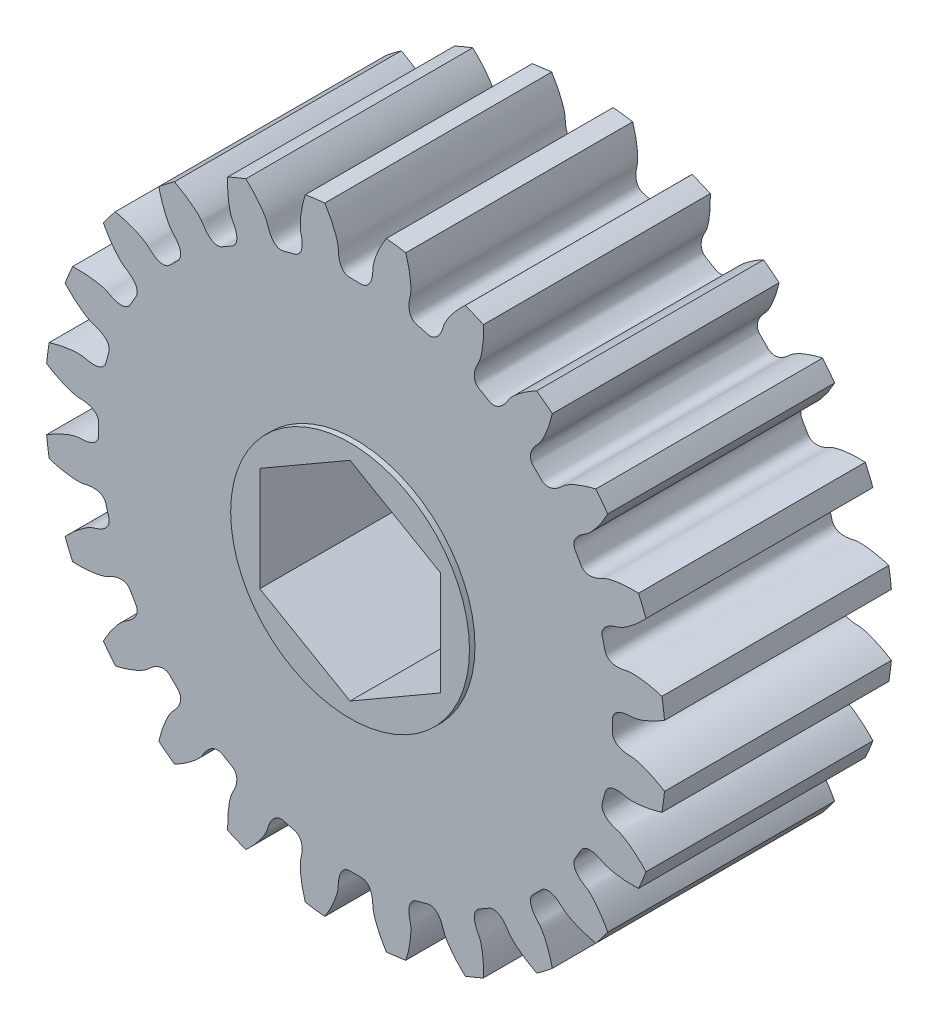
SolidWorks part; units mm, degrees
ref_plane "Front Plane" through (0, 0, 0) normal (0, 0, 1) x (1, 0, 0)
ref_plane "Top Plane" through (0, 0, 0) normal (0, 1, 0) x (1, 0, 0)
ref_plane "Right Plane" through (0, 0, 0) normal (1, 0, 0) x (0, 0, -1)
ref_plane "Plane1" through (0, 0, -6.0325) normal (0, 0, -1) x (-1, 0, 0)
sketch "Sketch1" plane through (0, 0, -6.0325) normal (0, 0, -1) x (-1, 0, 0)
  arc A0 (-12.7729, 10.461) -> (-13.4104, 9.6302) centre (0, 0) ccw
  arc A1 (-15.0452, 6.7987) -> (-15.446, 5.8312) centre (0, 0) ccw
  arc A2 (-16.2922, 2.673) -> (-16.4289, 1.6348) centre (0, 0) ccw
  arc A3 (-16.4289, -1.6348) -> (-16.2922, -2.673) centre (0, 0) ccw
  arc A4 (-15.446, -5.8312) -> (-15.0452, -6.7987) centre (0, 0) ccw
  arc A5 (-13.4104, -9.6302) -> (-12.7729, -10.461) centre (0, 0) ccw
  arc A6 (-10.461, -12.7729) -> (-9.6302, -13.4104) centre (0, 0) ccw
  arc A7 (-6.7987, -15.0452) -> (-5.8312, -15.446) centre (0, 0) ccw
  arc A8 (-2.673, -16.2922) -> (-1.6348, -16.4289) centre (0, 0) ccw
  arc A9 (1.6348, -16.4289) -> (2.673, -16.2922) centre (0, 0) ccw
  arc A10 (5.8312, -15.446) -> (6.7987, -15.0452) centre (0, 0) ccw
  arc A11 (9.6302, -13.4104) -> (10.461, -12.7729) centre (0, 0) ccw
  arc A12 (12.7729, -10.461) -> (13.4104, -9.6302) centre (0, 0) ccw
  arc A13 (15.0452, -6.7987) -> (15.446, -5.8312) centre (0, 0) ccw
  arc A14 (16.2922, -2.673) -> (16.4289, -1.6348) centre (0, 0) ccw
  arc A15 (16.4289, 1.6348) -> (16.2922, 2.673) centre (0, 0) ccw
  arc A16 (15.446, 5.8312) -> (15.0452, 6.7987) centre (0, 0) ccw
  arc A17 (13.4104, 9.6302) -> (12.7729, 10.461) centre (0, 0) ccw
  arc A18 (10.461, 12.7729) -> (9.6302, 13.4104) centre (0, 0) ccw
  arc A19 (6.7987, 15.0452) -> (5.8312, 15.446) centre (0, 0) ccw
  arc A20 (2.673, 16.2922) -> (1.6348, 16.4289) centre (0, 0) ccw
  arc A21 (-1.6348, 16.4289) -> (-2.673, 16.2922) centre (0, 0) ccw
  arc A22 (-5.8312, 15.446) -> (-6.7987, 15.0452) centre (0, 0) ccw
  arc A23 (-9.6302, 13.4104) -> (-10.461, 12.7729) centre (0, 0) ccw
  spline S0 degree 3 number of poles 101 (-15.0452, 6.7987) -> (-13.4104, 9.6302)
  spline S1 degree 3 number of poles 101 (-16.2922, 2.673) -> (-15.446, 5.8312)
  spline S2 degree 3 number of poles 101 (-16.4289, -1.6348) -> (-16.4289, 1.6348)
  spline S3 degree 3 number of poles 101 (-15.446, -5.8312) -> (-16.2922, -2.673)
  spline S4 degree 3 number of poles 101 (-13.4104, -9.6302) -> (-15.0452, -6.7987)
  spline S5 degree 3 number of poles 101 (-10.461, -12.7729) -> (-12.7729, -10.461)
  spline S6 degree 3 number of poles 101 (-6.7987, -15.0452) -> (-9.6302, -13.4104)
  spline S7 degree 3 number of poles 101 (-2.673, -16.2922) -> (-5.8312, -15.446)
  spline S8 degree 3 number of poles 101 (1.6348, -16.4289) -> (-1.6348, -16.4289)
  spline S9 degree 3 number of poles 101 (5.8312, -15.446) -> (2.673, -16.2922)
  spline S10 degree 3 number of poles 101 (9.6302, -13.4104) -> (6.7987, -15.0452)
  spline S11 degree 3 number of poles 101 (12.7729, -10.461) -> (10.461, -12.7729)
  spline S12 degree 3 number of poles 101 (15.0452, -6.7987) -> (13.4104, -9.6302)
  spline S13 degree 3 number of poles 101 (16.2922, -2.673) -> (15.446, -5.8312)
  spline S14 degree 3 number of poles 101 (16.4289, 1.6348) -> (16.4289, -1.6348)
  spline S15 degree 3 number of poles 101 (15.446, 5.8312) -> (16.2922, 2.673)
  spline S16 degree 3 number of poles 101 (13.4104, 9.6302) -> (15.0452, 6.7987)
  spline S17 degree 3 number of poles 101 (10.461, 12.7729) -> (12.7729, 10.461)
  spline S18 degree 3 number of poles 101 (6.7987, 15.0452) -> (9.6302, 13.4104)
  spline S19 degree 3 number of poles 101 (2.673, 16.2922) -> (5.8312, 15.446)
  spline S20 degree 3 number of poles 101 (-1.6348, 16.4289) -> (1.6348, 16.4289)
  spline S21 degree 3 number of poles 101 (-5.8312, 15.446) -> (-2.673, 16.2922)
  spline S22 degree 3 number of poles 101 (-9.6302, 13.4104) -> (-6.7987, 15.0452)
  spline S23 degree 3 number of poles 101 (-12.7729, 10.461) -> (-10.461, 12.7729)
extrude "Boss-Extrude1" add sketch "Sketch1" against normal blind 12.065
sketch "Sketch2" plane through (0, 0, -6.0325) normal (0, 0, -1) x (-1, 0, 0)
  circle A0 centre (0, 0) radius 6.35
extrude "Boss-Extrude2" add sketch "Sketch2" along normal blind 0.2921
sketch "Sketch3" plane through (0, 0, 6.0325) normal (0, 0, 1) x (1, 0, 0)
  circle A0 centre (0, 0) radius 6.35
extrude "Boss-Extrude3" add sketch "Sketch3" along normal blind 0.2921
sketch "Sketch4" plane through (0, 0, 6.3246) normal (0, 0, 1) x (1, 0, 0)
  line L0 (4.8006, -2.7716) -> (4.8006, 2.7716)
  line L1 (4.8006, 2.7716) -> (0, 5.5433)
  line L2 (0, 5.5433) -> (-4.8006, 2.7716)
  line L3 (-4.8006, 2.7716) -> (-4.8006, -2.7716)
  line L4 (-4.8006, -2.7716) -> (0, -5.5433)
  line L5 (0, -5.5433) -> (4.8006, -2.7716)
extrude "Cut-Extrude1" cut sketch "Sketch4" against normal through all
